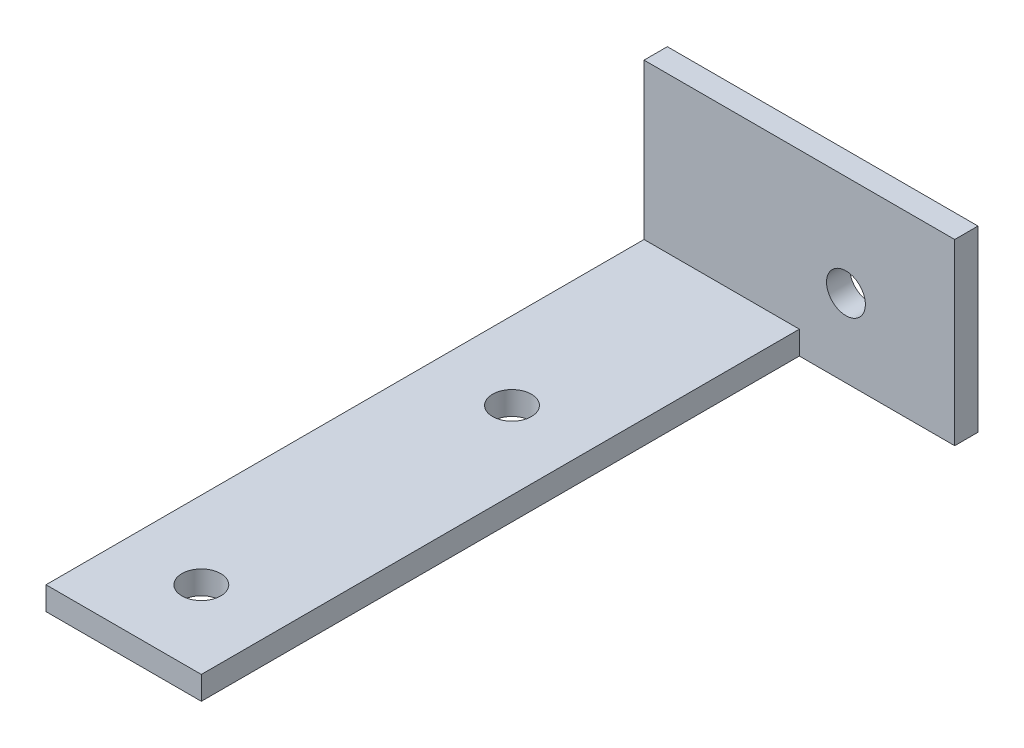
SolidWorks part; units mm, degrees
material "ABS"
ref_plane "Front Plane" through (0, 0, 0) normal (0, 0, 1) x (1, 0, 0)
ref_plane "Top Plane" through (0, 0, 0) normal (0, 1, 0) x (1, 0, 0)
ref_plane "Right Plane" through (0, 0, 0) normal (1, 0, 0) x (0, 0, -1)
sketch "Sketch1" plane through (0, 0, 0) normal (0, 1, 0) x (1, 0, 0)
  line L0 (0, 40) -> (0, -40) construction
  line L1 (-10, 40) -> (10, 40)
  line L2 (-10, 40) -> (-10, -40)
  line L3 (-10, -40) -> (10, -40)
  line L4 (10, 40) -> (10, -40)
  line L5 (-10, 40) -> (10, -40) construction
  line L6 (-10, -40) -> (10, 40) construction
  circle A1 centre (0, -30) radius 2.5
  circle A2 centre (0, 10) radius 2.5
  point P0 (0, 0)
  point P8 (0, -30.4782)
  point P9 (0, 9.784)
  point P14 (0, 0)
  point P15 (0, 12.7506)
extrude "Boss-Extrude1" add sketch "Sketch1" along normal blind 3
sketch "Sketch2" plane through (0, 3, 0) normal (0, 1, 0) x (1, 0, 0)
  line L0 (10, -40) -> (10, 40) construction
  line L1 (-10, 40) -> (10, 40)
  line L2 (-10, 40) -> (-10, 37)
  line L3 (-10, 37) -> (10, 37)
  line L4 (10, 40) -> (10, 37)
extrude "Boss-Extrude2" add sketch "Sketch2" along normal blind 20
sketch "Sketch8" plane through (10, 0, 0) normal (1, 0, 0) x (0, 0, -1)
  line L1 (37, 23) -> (40, 23)
  line L2 (37, 23) -> (37, 0)
  line L3 (37, 0) -> (40, 0)
  line L4 (40, 23) -> (40, 0)
extrude "Boss-Extrude5" add sketch "Sketch8" along normal blind 20
sketch "Sketch9" plane through (0, 0, -40) normal (0, 0, -1) x (-1, 0, 0)
  line L0 (0, 23) -> (0, 0) construction
  line L1 (-30, 23) -> (10, 23) construction
  circle A0 centre (-16, 10) radius 2.5
  point P7 (0, 11.9211)
extrude "Cut-Extrude3" cut sketch "Sketch9" against normal blind 20
